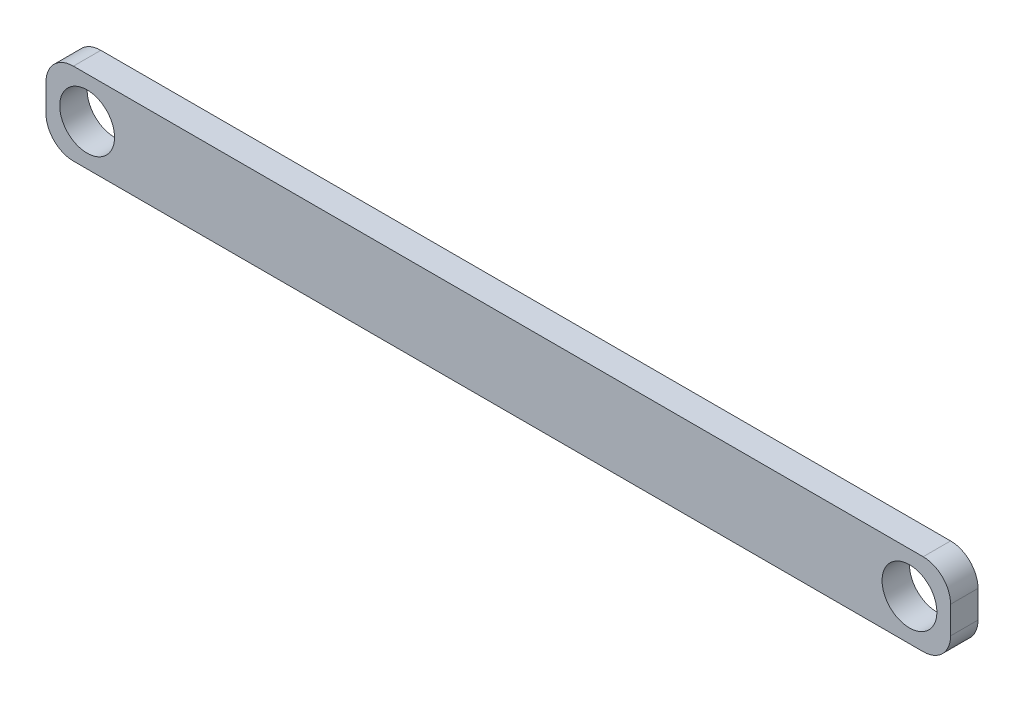
SolidWorks part; units mm, degrees
ref_plane "Alzado" through (0, 0, 0) normal (0, 0, 1) x (1, 0, 0)
ref_plane "Planta" through (0, 0, 0) normal (0, 1, 0) x (1, 0, 0)
ref_plane "Vista lateral" through (0, 0, 0) normal (1, 0, 0) x (0, 0, -1)
sketch "Croquis1" plane through (0, 0, 0) normal (0, 0, 1) x (1, 0, 0)
  line L1 (-155, 15) -> (155, 15)
  line L2 (-165, 5) -> (-165, -5)
  line L3 (-155, -15) -> (155, -15)
  line L4 (165, 5) -> (165, -5)
  line L5 (-165, 15) -> (165, -15) construction
  line L6 (-165, -15) -> (165, 15) construction
  circle A0 centre (-150, 0) radius 10
  circle A1 centre (150, 0) radius 10
  arc A2 (155, 15) -> (165, 5) centre (155, 5) cw
  arc A3 (165, -5) -> (155, -15) centre (155, -5) cw
  arc A4 (-155, -15) -> (-165, -5) centre (-155, -5) cw
  arc A5 (-155, 15) -> (-165, 5) centre (-155, 5) ccw
  point P0 (0, 0)
  dimension "D1" = 10
  dimension "D2" = 330
  dimension "D3" = 150
  dimension "D4" = 150
extrude "Saliente-Extruir1" add sketch "Croquis1" along normal mid plane 10
